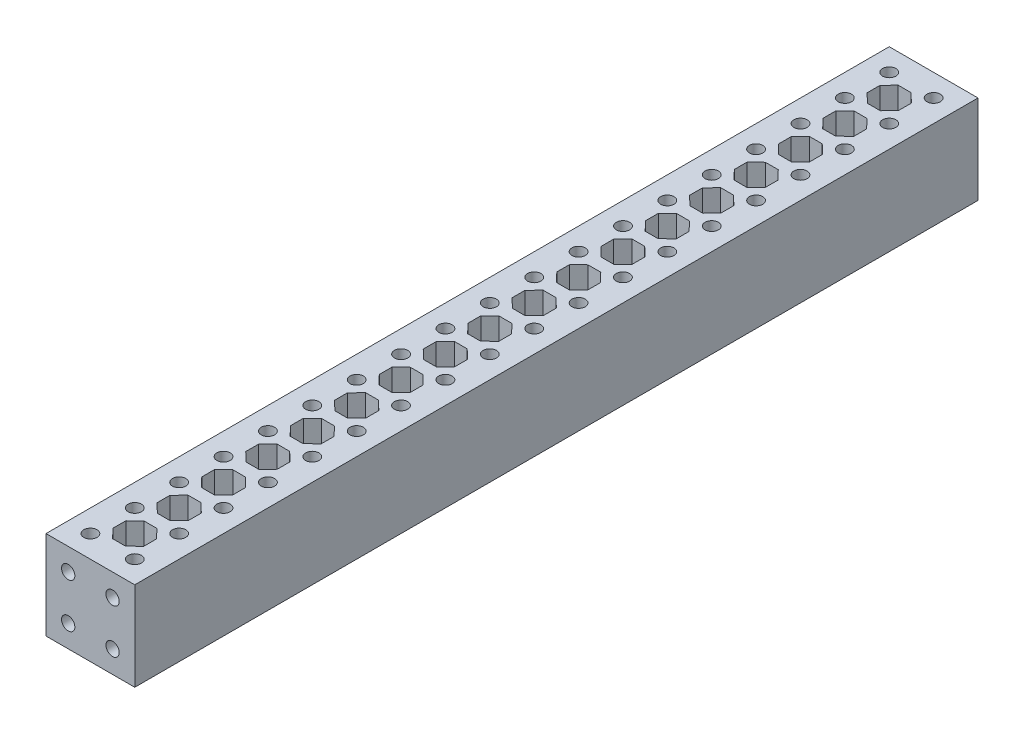
SolidWorks part; units mm, degrees
ref_plane "Front Plane" through (0, 0, 0) normal (0, 0, 1) x (1, 0, 0)
ref_plane "Top Plane" through (0, 0, 0) normal (0, 1, 0) x (1, 0, 0)
ref_plane "Right Plane" through (0, 0, 0) normal (1, 0, 0) x (0, 0, -1)
sketch "Sketch1" plane through (0, 0, 0) normal (0, 0, 1) x (1, 0, 0)
  line L1 (0, 0) -> (20, 0)
  line L2 (0, 0) -> (0, 20)
  line L3 (0, 20) -> (20, 20)
  line L4 (20, 0) -> (20, 20)
  dimension "D1" = 20
  dimension "D2" = 20
extrude "Boss-Extrude1" add sketch "Sketch1" along normal blind 190
sketch "Sketch2" plane through (0, 20, 0) normal (0, 1, 0) x (1, 0, 0)
  line L0 (20, -190) -> (20, 0) construction
  line L1 (20, -190) -> (0, -190) construction
  line L2 (20, -180) -> (9.1507, -180) construction
  line L3 (20, -170) -> (8.1861, -170) construction
  line L4 (20, -160) -> (8.5262, -160) construction
  line L5 (20, -150) -> (8.7307, -150) construction
  line L6 (20, -140) -> (9.1507, -140) construction
  line L7 (20, -130) -> (7.6382, -130) construction
  line L8 (20, -120) -> (8.5262, -120) construction
  line L9 (20, -110) -> (9.3805, -110) construction
  line L10 (20, -100) -> (9.8514, -100) construction
  line L11 (20, -90) -> (9.1507, -90) construction
  line L12 (20, -80) -> (12.2715, -80) construction
  line L13 (20, -70) -> (10.5723, -70) construction
  line L14 (20, -60) -> (7.6382, -60) construction
  line L15 (20, -50) -> (7.6382, -50) construction
  line L16 (20, -40) -> (9.8514, -40) construction
  line L17 (20, -30) -> (5.8594, -30) construction
  line L18 (20, -20) -> (9.1507, -20) construction
  line L19 (20, -10) -> (9.1507, -10) construction
  line L20 (8.5, -183.5) -> (11.4, -183.5)
  line L21 (10, -190) -> (10, -183.8181) construction
  line L22 (11.4, -183.5) -> (13.5, -181.5)
  line L23 (13.5, -181.5) -> (13.5, -178.6)
  line L24 (13.5, -178.6) -> (11.5, -176.5)
  line L25 (11.5, -176.5) -> (8.6, -176.5)
  line L26 (8.6, -176.5) -> (6.5, -178.5)
  line L27 (6.5, -178.5) -> (6.5, -181.4)
  line L28 (6.5, -181.4) -> (8.5, -183.5)
  line L29 (0, -190) -> (0, 0) construction
  line L30 (5, -175) -> (-3.0566, -175) construction
  line L31 (5, -165) -> (-3.8812, -165) construction
  line L32 (5, -155) -> (-2.3547, -155) construction
  line L33 (5, -145) -> (-1.953, -145) construction
  line L34 (5, -135) -> (-3.5529, -135) construction
  line L35 (5, -125) -> (-3.8812, -125) construction
  line L36 (5, -115) -> (-5.8894, -115) construction
  line L37 (5, -105) -> (-3.0566, -105) construction
  line L38 (5, -95) -> (-3.8812, -95) construction
  line L39 (5, -85) -> (-2.3547, -85) construction
  line L40 (-2.3547, -85) -> (-2.3547, -75) construction
  line L41 (-2.3547, -75) -> (5, -75) construction
  line L42 (5, -75) -> (5, -65) construction
  line L43 (5, -65) -> (-2.3547, -65) construction
  line L44 (-2.3547, -65) -> (-2.3547, -55) construction
  line L45 (-2.3547, -55) -> (5, -55) construction
  line L46 (5, -55) -> (5, -45) construction
  line L47 (5, -45) -> (-3.8812, -45) construction
  line L48 (-3.8812, -45) -> (-3.8812, -35) construction
  line L49 (-3.8812, -35) -> (5, -35) construction
  line L50 (5, -35) -> (5, -25) construction
  line L51 (5, -25) -> (-4.9811, -25) construction
  line L52 (-4.9811, -25) -> (-4.9811, -15) construction
  line L53 (-4.9811, -15) -> (5, -15) construction
  line L54 (5, -15) -> (5, -5) construction
  line L55 (5, -5) -> (-3.8812, -5) construction
  line L56 (6.5, -171.5) -> (6.5, -168.6)
  line L57 (8.6, -173.5) -> (6.5, -171.5)
  line L58 (11.5, -173.5) -> (8.6, -173.5)
  line L59 (13.5, -171.4) -> (11.5, -173.5)
  line L60 (13.5, -168.5) -> (13.5, -171.4)
  line L61 (11.4, -166.5) -> (13.5, -168.5)
  line L62 (8.5, -166.5) -> (11.4, -166.5)
  line L63 (6.5, -168.6) -> (8.5, -166.5)
  line L64 (8.6, -156.5) -> (6.5, -158.5)
  line L65 (11.5, -156.5) -> (8.6, -156.5)
  line L66 (13.5, -158.6) -> (11.5, -156.5)
  line L67 (13.5, -161.5) -> (13.5, -158.6)
  line L68 (11.4, -163.5) -> (13.5, -161.5)
  line L69 (8.5, -163.5) -> (11.4, -163.5)
  line L70 (6.5, -161.4) -> (8.5, -163.5)
  line L71 (6.5, -158.5) -> (6.5, -161.4)
  line L72 (11.5, -153.5) -> (8.6, -153.5)
  line L73 (13.5, -151.4) -> (11.5, -153.5)
  line L74 (13.5, -148.5) -> (13.5, -151.4)
  line L75 (11.4, -146.5) -> (13.5, -148.5)
  line L76 (8.5, -146.5) -> (11.4, -146.5)
  line L77 (6.5, -148.6) -> (8.5, -146.5)
  line L78 (6.5, -151.5) -> (6.5, -148.6)
  line L79 (8.6, -153.5) -> (6.5, -151.5)
  line L80 (13.5, -138.6) -> (11.5, -136.5)
  line L81 (13.5, -141.5) -> (13.5, -138.6)
  line L82 (11.4, -143.5) -> (13.5, -141.5)
  line L83 (8.5, -143.5) -> (11.4, -143.5)
  line L84 (6.5, -141.4) -> (8.5, -143.5)
  line L85 (6.5, -138.5) -> (6.5, -141.4)
  line L86 (8.6, -136.5) -> (6.5, -138.5)
  line L87 (11.5, -136.5) -> (8.6, -136.5)
  line L88 (13.5, -128.5) -> (13.5, -131.4)
  line L89 (11.4, -126.5) -> (13.5, -128.5)
  line L90 (8.5, -126.5) -> (11.4, -126.5)
  line L91 (6.5, -128.6) -> (8.5, -126.5)
  line L92 (6.5, -131.5) -> (6.5, -128.6)
  line L93 (8.6, -133.5) -> (6.5, -131.5)
  line L94 (11.5, -133.5) -> (8.6, -133.5)
  line L95 (13.5, -131.4) -> (11.5, -133.5)
  line L96 (11.4, -123.5) -> (13.5, -121.5)
  line L97 (8.5, -123.5) -> (11.4, -123.5)
  line L98 (6.5, -121.4) -> (8.5, -123.5)
  line L99 (6.5, -118.5) -> (6.5, -121.4)
  line L100 (8.6, -116.5) -> (6.5, -118.5)
  line L101 (11.5, -116.5) -> (8.6, -116.5)
  line L102 (13.5, -118.6) -> (11.5, -116.5)
  line L103 (13.5, -121.5) -> (13.5, -118.6)
  line L104 (8.5, -106.5) -> (11.4, -106.5)
  line L105 (6.5, -108.6) -> (8.5, -106.5)
  line L106 (6.5, -111.5) -> (6.5, -108.6)
  line L107 (8.6, -113.5) -> (6.5, -111.5)
  line L108 (11.5, -113.5) -> (8.6, -113.5)
  line L109 (13.5, -111.4) -> (11.5, -113.5)
  line L110 (13.5, -108.5) -> (13.5, -111.4)
  line L111 (11.4, -106.5) -> (13.5, -108.5)
  line L112 (6.5, -101.4) -> (8.5, -103.5)
  line L113 (6.5, -98.5) -> (6.5, -101.4)
  line L114 (8.6, -96.5) -> (6.5, -98.5)
  line L115 (11.5, -96.5) -> (8.6, -96.5)
  line L116 (13.5, -98.6) -> (11.5, -96.5)
  line L117 (13.5, -101.5) -> (13.5, -98.6)
  line L118 (11.4, -103.5) -> (13.5, -101.5)
  line L119 (8.5, -103.5) -> (11.4, -103.5)
  line L120 (6.5, -91.5) -> (6.5, -88.6)
  line L121 (8.6, -93.5) -> (6.5, -91.5)
  line L122 (11.5, -93.5) -> (8.6, -93.5)
  line L123 (13.5, -91.4) -> (11.5, -93.5)
  line L124 (13.5, -88.5) -> (13.5, -91.4)
  line L125 (11.4, -86.5) -> (13.5, -88.5)
  line L126 (8.5, -86.5) -> (11.4, -86.5)
  line L127 (6.5, -88.6) -> (8.5, -86.5)
  line L128 (8.6, -76.5) -> (6.5, -78.5)
  line L129 (11.5, -76.5) -> (8.6, -76.5)
  line L130 (13.5, -78.6) -> (11.5, -76.5)
  line L131 (13.5, -81.5) -> (13.5, -78.6)
  line L132 (11.4, -83.5) -> (13.5, -81.5)
  line L133 (8.5, -83.5) -> (11.4, -83.5)
  line L134 (6.5, -81.4) -> (8.5, -83.5)
  line L135 (6.5, -78.5) -> (6.5, -81.4)
  line L136 (11.5, -73.5) -> (8.6, -73.5)
  line L137 (13.5, -71.4) -> (11.5, -73.5)
  line L138 (13.5, -68.5) -> (13.5, -71.4)
  line L139 (11.4, -66.5) -> (13.5, -68.5)
  line L140 (8.5, -66.5) -> (11.4, -66.5)
  line L141 (6.5, -68.6) -> (8.5, -66.5)
  line L142 (6.5, -71.5) -> (6.5, -68.6)
  line L143 (8.6, -73.5) -> (6.5, -71.5)
  line L144 (13.5, -58.6) -> (11.5, -56.5)
  line L145 (13.5, -61.5) -> (13.5, -58.6)
  line L146 (11.4, -63.5) -> (13.5, -61.5)
  line L147 (8.5, -63.5) -> (11.4, -63.5)
  line L148 (6.5, -61.4) -> (8.5, -63.5)
  line L149 (6.5, -58.5) -> (6.5, -61.4)
  line L150 (8.6, -56.5) -> (6.5, -58.5)
  line L151 (11.5, -56.5) -> (8.6, -56.5)
  line L152 (13.5, -48.5) -> (13.5, -51.4)
  line L153 (11.4, -46.5) -> (13.5, -48.5)
  line L154 (8.5, -46.5) -> (11.4, -46.5)
  line L155 (6.5, -48.6) -> (8.5, -46.5)
  line L156 (6.5, -51.5) -> (6.5, -48.6)
  line L157 (8.6, -53.5) -> (6.5, -51.5)
  line L158 (11.5, -53.5) -> (8.6, -53.5)
  line L159 (13.5, -51.4) -> (11.5, -53.5)
  line L160 (11.4, -43.5) -> (13.5, -41.5)
  line L161 (8.5, -43.5) -> (11.4, -43.5)
  line L162 (6.5, -41.4) -> (8.5, -43.5)
  line L163 (6.5, -38.5) -> (6.5, -41.4)
  line L164 (8.6, -36.5) -> (6.5, -38.5)
  line L165 (11.5, -36.5) -> (8.6, -36.5)
  line L166 (13.5, -38.6) -> (11.5, -36.5)
  line L167 (13.5, -41.5) -> (13.5, -38.6)
  line L168 (8.5, -26.5) -> (11.4, -26.5)
  line L169 (6.5, -28.6) -> (8.5, -26.5)
  line L170 (6.5, -31.5) -> (6.5, -28.6)
  line L171 (8.6, -33.5) -> (6.5, -31.5)
  line L172 (11.5, -33.5) -> (8.6, -33.5)
  line L173 (13.5, -31.4) -> (11.5, -33.5)
  line L174 (13.5, -28.5) -> (13.5, -31.4)
  line L175 (11.4, -26.5) -> (13.5, -28.5)
  line L176 (6.5, -21.4) -> (8.5, -23.5)
  line L177 (6.5, -18.5) -> (6.5, -21.4)
  line L178 (8.6, -16.5) -> (6.5, -18.5)
  line L179 (11.5, -16.5) -> (8.6, -16.5)
  line L180 (13.5, -18.6) -> (11.5, -16.5)
  line L181 (13.5, -21.5) -> (13.5, -18.6)
  line L182 (11.4, -23.5) -> (13.5, -21.5)
  line L183 (8.5, -23.5) -> (11.4, -23.5)
  line L184 (6.5, -11.5) -> (6.5, -8.6)
  line L185 (8.6, -13.5) -> (6.5, -11.5)
  line L186 (11.5, -13.5) -> (8.6, -13.5)
  line L187 (13.5, -11.4) -> (11.5, -13.5)
  line L188 (13.5, -8.5) -> (13.5, -11.4)
  line L189 (11.4, -6.5) -> (13.5, -8.5)
  line L190 (8.5, -6.5) -> (11.4, -6.5)
  line L191 (6.5, -8.6) -> (8.5, -6.5)
  circle A0 centre (15, -185) radius 1.5
  circle A1 centre (15, -175) radius 1.5
  circle A2 centre (15, -165) radius 1.5
  circle A3 centre (15, -155) radius 1.5
  circle A4 centre (15, -145) radius 1.5
  circle A5 centre (15, -135) radius 1.5
  circle A6 centre (15, -125) radius 1.5
  circle A7 centre (15, -115) radius 1.5
  circle A8 centre (15, -105) radius 1.5
  circle A9 centre (15, -95) radius 1.5
  circle A10 centre (15, -85) radius 1.5
  circle A11 centre (15, -75) radius 1.5
  circle A12 centre (15, -65) radius 1.5
  circle A13 centre (15, -55) radius 1.5
  circle A14 centre (15, -45) radius 1.5
  circle A15 centre (15, -35) radius 1.5
  circle A16 centre (15, -25) radius 1.5
  circle A17 centre (15, -15) radius 1.5
  circle A18 centre (15, -5) radius 1.5
  circle A19 centre (5, -5) radius 1.5
  circle A20 centre (5, -15) radius 1.5
  circle A21 centre (5, -25) radius 1.5
  circle A22 centre (5, -35) radius 1.5
  circle A23 centre (5, -45) radius 1.5
  circle A24 centre (5, -55) radius 1.5
  circle A25 centre (5, -65) radius 1.5
  circle A26 centre (5, -75) radius 1.5
  circle A27 centre (5, -85) radius 1.5
  circle A28 centre (5, -95) radius 1.5
  circle A29 centre (5, -105) radius 1.5
  circle A30 centre (5, -115) radius 1.5
  circle A31 centre (5, -125) radius 1.5
  circle A32 centre (5, -135) radius 1.5
  circle A33 centre (5, -145) radius 1.5
  circle A34 centre (5, -155) radius 1.5
  circle A35 centre (5, -165) radius 1.5
  circle A36 centre (5, -175) radius 1.5
  circle A37 centre (5, -185) radius 1.5
  dimension "D1" = 3
  dimension "D2" = 5
  dimension "D3" = 5
  dimension "D4" = 5
  dimension "D5" = 5
  dimension "D6" = 5
  dimension "D7" = 5
  dimension "D8" = 5
  dimension "D9" = 5
  dimension "D10" = 5
  dimension "D11" = 5
  dimension "D12" = 5
  dimension "D13" = 5
  dimension "D14" = 5
  dimension "D15" = 5
  dimension "D16" = 5
  dimension "D17" = 5
  dimension "D18" = 5
  dimension "D19" = 5
  dimension "D20" = 5
  dimension "D21" = 5
  dimension "D22" = 6.5
  dimension "D23" = 6.5
  dimension "D24" = 6.5
  dimension "D25" = 2.9
  dimension "D26" = 2.9
  dimension "D27" = 2.9
  dimension "D28" = 2.9
  dimension "D29" = 2.9
  dimension "D30" = 2.9
  dimension "D31" = 2.9
  dimension "D32" = 2.9
sketch "Sketch3" plane through (0, 0, 190) normal (0, 0, 1) x (1, 0, 0)
  line L0 (20, 20) -> (9.1507, 20) construction
  line L2 (20, 0) -> (20, 20) construction
  line L3 (20, 10) -> (11.9367, 10) construction
  line L4 (10, 0) -> (10, 7.5858) construction
  line L5 (0, 0) -> (20, 0) construction
  circle A0 centre (15, 15) radius 1.5
  circle A1 centre (15, 5) radius 1.5
  circle A2 centre (5, 5) radius 1.5
  circle A3 centre (5, 15) radius 1.5
  dimension "D3" = 3
  dimension "D1" = 5
  dimension "D2" = 5
extrude "Cut-Extrude2" cut sketch "Sketch2" against normal blind 20
extrude "Cut-Extrude3" cut sketch "Sketch3" against normal blind 5
